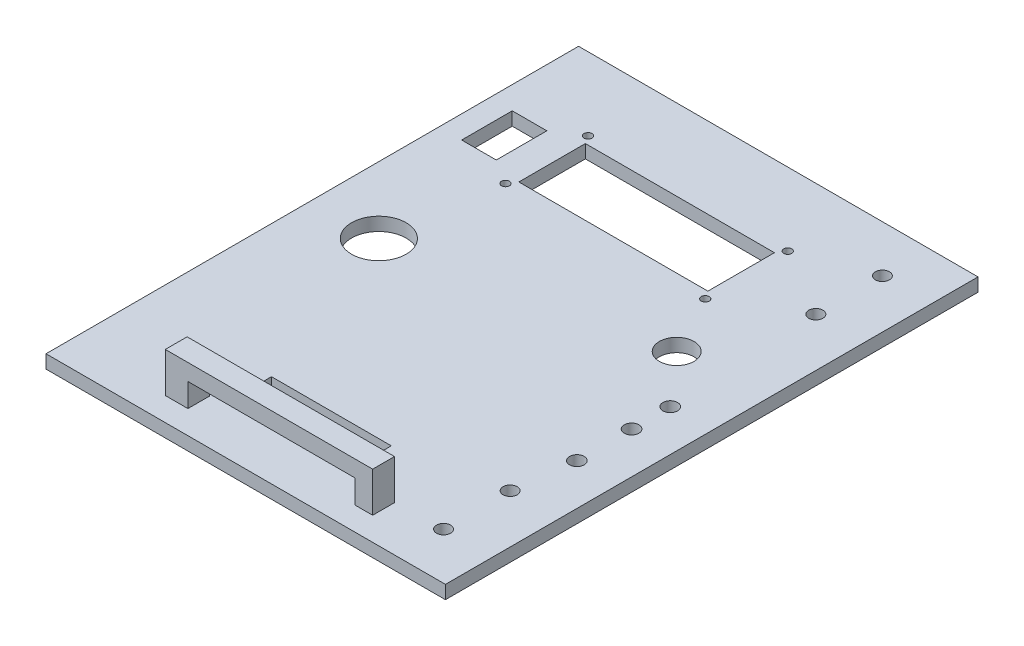
SolidWorks part; units mm, degrees
ref_plane "Front Plane" through (0, 0, 0) normal (0, 0, 1) x (1, 0, 0)
ref_plane "Top Plane" through (0, 0, 0) normal (0, 1, 0) x (1, 0, 0)
ref_plane "Right Plane" through (0, 0, 0) normal (1, 0, 0) x (0, 0, -1)
sketch "Sketch1" plane through (0, 0, 0) normal (0, 1, 0) x (1, 0, 0)
  line L1 (-75, 100) -> (75, 100)
  line L2 (-75, 100) -> (-75, -100)
  line L3 (-75, -100) -> (75, -100)
  line L4 (75, 100) -> (75, -100)
  line L5 (-75, 100) -> (75, -100) construction
  line L6 (-75, -100) -> (75, 100) construction
  point P0 (0, 0)
  dimension "D1" = 150
  dimension "D2" = 200
extrude "Boss-Extrude1" add sketch "Sketch1" along normal blind 5
sketch "Sketch2" plane through (0, 5, 0) normal (0, 1, 0) x (1, 0, 0)
  line L0 (-75, 100) -> (-75, -100) construction
  line L1 (75, 100) -> (-75, 100) construction
  line L2 (75, -100) -> (75, 100) construction
  line L3 (75, 0) -> (0, 0) construction
  circle A0 centre (-50, 0) radius 10.25
  circle A1 centre (56.7, 82.4) radius 2.65
  circle A2 centre (56.7, 57.4) radius 2.65
  circle A3 centre (56.7, -57.4) radius 2.65
  circle A4 centre (56.7, -82.4) radius 2.65
  dimension "D1" = 20.5
  dimension "D4" = 5.3
  dimension "D7" = 5.3
  dimension "D2" = 25
  dimension "D3" = 100
  dimension "D5" = 17.6
  dimension "D6" = 18.3
  dimension "D8" = 25
extrude "Cut-Extrude1" cut sketch "Sketch2" against normal up to next
sketch "Sketch3" plane through (0, 5, 0) normal (0, 1, 0) x (1, 0, 0)
  line L0 (-42.0869, 69.6442) -> (28.9131, 69.6442)
  line L1 (-42.0869, 69.6442) -> (-42.0869, 44.6442)
  line L2 (-42.0869, 44.6442) -> (28.9131, 44.6442)
  line L3 (28.9131, 69.6442) -> (28.9131, 44.6442)
  line L4 (-25.2093, -65.1134) -> (19.7907, -65.1134)
  line L5 (-25.2093, -65.1134) -> (-25.2093, -70.1134)
  line L6 (-25.2093, -70.1134) -> (19.7907, -70.1134)
  line L7 (19.7907, -65.1134) -> (19.7907, -70.1134)
  line L9 (-66.462, 66.554) -> (-53.462, 66.554)
  line L10 (-66.462, 66.554) -> (-66.462, 47.554)
  line L11 (-66.462, 47.554) -> (-53.462, 47.554)
  line L12 (-53.462, 66.554) -> (-53.462, 47.554)
  circle A0 centre (-44.0869, 72.6442) radius 1.5
  circle A1 centre (-44.0869, 41.6442) radius 1.5
  circle A2 centre (30.9131, 72.6442) radius 1.5
  circle A3 centre (30.9131, 41.6442) radius 1.5
  circle A4 centre (42.6668, 19.1751) radius 6.5
  circle A6 centre (59.4281, 0) radius 2.75
  circle A7 centre (59.4281, -14.5237) radius 2.75
  circle A8 centre (59.4281, -35.0822) radius 2.75
  point P0 (-6.5869, 57.1442)
  point P29 (0, 0)
  point P30 (59.4281, 0)
  point P31 (59.4281, -14.5237)
  point P32 (59.4281, -35.0822)
  dimension "D3" = 3
  dimension "D4" = 3
  dimension "D5" = 3
  dimension "D6" = 3
  dimension "D13" = 13
  dimension "D14" = 5.5
  dimension "D15" = 5.5
  dimension "D16" = 5.5
  dimension "D1" = 71
  dimension "D2" = 25
  dimension "D7" = 75
  dimension "D8" = 31
  dimension "D9" = 5
  dimension "D10" = 45
  dimension "D11" = 19
  dimension "D12" = 13
extrude "Cut-Extrude2" cut sketch "Sketch3" against normal blind 10
sketch "Sketch4" plane through (0, 5, 0) normal (0, 1, 0) x (1, 0, 0)
  line L1 (-39.0101, -82.9943) -> (38.8611, -82.9943)
  line L2 (-39.0101, -82.9943) -> (-39.0101, -91.1913)
  line L3 (-39.0101, -91.1913) -> (38.8611, -91.1913)
  line L4 (38.8611, -82.9943) -> (38.8611, -91.1913)
extrude "Boss-Extrude2" add sketch "Sketch4" along normal blind 15
sketch "Sketch5" plane through (0, 0, 91.1913) normal (0, 0, 1) x (1, 0, 0)
  line L0 (-39.0101, 5) -> (38.8611, 5) construction
  line L1 (-30.5219, 5) -> (32.2223, 5)
  line L2 (-30.5219, 5) -> (-30.5219, 13.8259)
  line L3 (-30.5219, 13.8259) -> (32.2223, 13.8259)
  line L4 (32.2223, 5) -> (32.2223, 13.8259)
extrude "Cut-Extrude3" cut sketch "Sketch5" against normal blind 15
